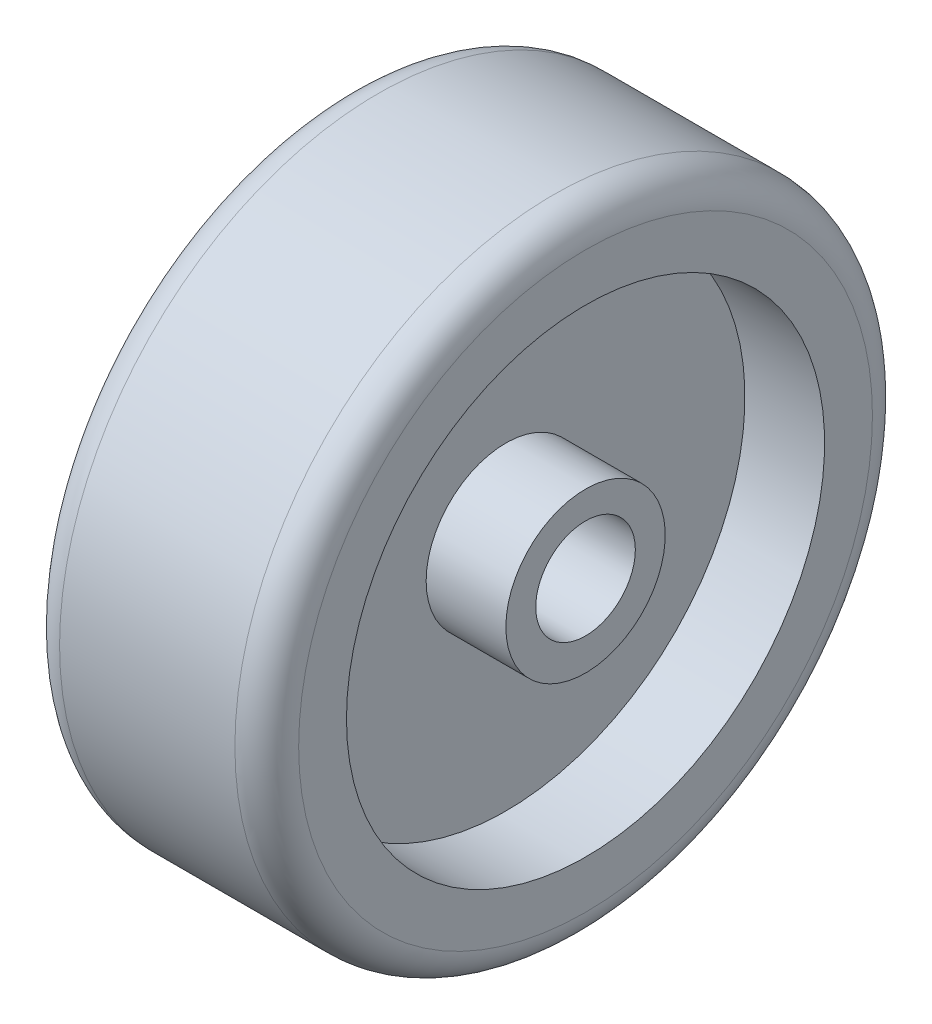
SolidWorks part; units mm, degrees
ref_plane "Front Plane" through (0, 0, 0) normal (0, 0, 1) x (1, 0, 0)
ref_plane "Top Plane" through (0, 0, 0) normal (0, 1, 0) x (1, 0, 0)
ref_plane "Right Plane" through (0, 0, 0) normal (1, 0, 0) x (0, 0, -1)
sketch "Sketch1" plane through (0, 0, 0) normal (0, 0, 1) x (1, 0, 0)
  line L0 (0, 0) -> (0, 88.0925) construction
  line L1 (0, 0) -> (-72.3706, 0) construction
  line L2 (-38.1, -0.7295) -> (-38.1, 24.6705)
  line L3 (-38.1, 24.6705) -> (-12.7, 24.6705)
  line L4 (-12.7, 24.6705) -> (-12.7, 75.4705)
  line L5 (-12.7, 75.4705) -> (-38.1, 75.4705)
  line L6 (-38.1, 75.4705) -> (-38.1, 100.8705)
  line L7 (38.1, 75.4705) -> (38.1, 100.8705)
  line L8 (12.7, 75.4705) -> (38.1, 75.4705)
  line L9 (12.7, 24.6705) -> (12.7, 75.4705)
  line L10 (38.1, 24.6705) -> (12.7, 24.6705)
  line L11 (38.1, -0.7295) -> (38.1, 24.6705)
  line L12 (-38.1, 100.8705) -> (38.1, 100.8705)
  line L13 (-38.1, -0.7295) -> (38.1, -0.7295)
  dimension "D1" = 76.2
  dimension "D2" = 76.2
  dimension "D3" = 25.4
  dimension "D4" = 50.8
  dimension "D5" = 25.4
  dimension "D6" = 25.4
revolve "Revolve2" add sketch "Sketch1" angle 360 about L13
sketch "Sketch2" plane through (38.1, 0, 0) normal (1, 0, 0) x (0, 0, -1)
  circle A0 centre (0, 0) radius 15.875
  dimension "D1" = 31.75
extrude "Cut-Extrude1" cut sketch "Sketch2" against normal through all
fillet "Fillet2" radius 10.16 1 edges at (38.1, -0.7295, 101.6)
fillet "Fillet3" radius 10.16 1 edges at (-38.1, -0.7295, 101.6)
